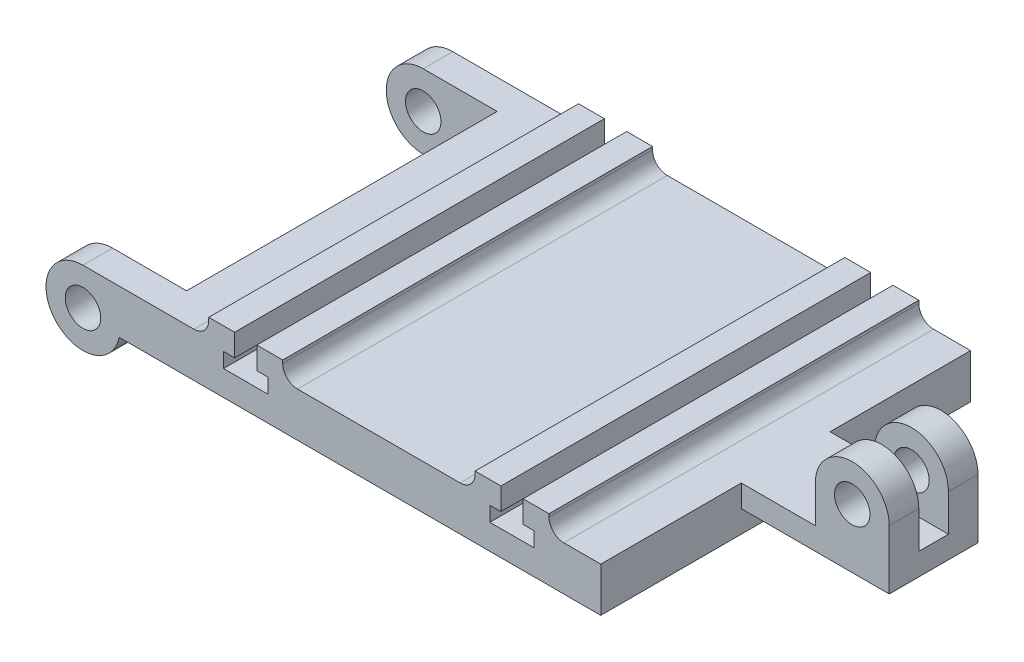
SolidWorks part; units mm, degrees
material "Ferro fundido maleável"
ref_plane "Plano frontal" through (0, 0, 0) normal (0, 0, 1) x (1, 0, 0)
ref_plane "Plano superior" through (0, 0, 0) normal (0, 1, 0) x (1, 0, 0)
ref_plane "Plano direito" through (0, 0, 0) normal (1, 0, 0) x (0, 0, -1)
sketch "Esboço1" plane through (0, 0, 0) normal (0, 1, 0) x (1, 0, 0)
  line L1 (-150, -125) -> (150, -125)
  line L2 (-150, -125) -> (-150, 125)
  line L3 (-150, 125) -> (150, 125)
  line L4 (150, -125) -> (150, 125)
  line L5 (-150, -125) -> (150, 125) construction
  line L6 (-150, 125) -> (150, -125) construction
  point P0 (0, 0)
  dimension "D1" = 300
  dimension "D2" = 250
extrude "Ressalto-extrusão1" add sketch "Esboço1" along normal blind 30
sketch "Esboço3" plane through (0, 30, 0) normal (0, 1, 0) x (1, 0, 0)
  line L0 (150, 125) -> (-150, 125) construction
  line L1 (115, 125) -> (65, 125)
  line L2 (115, 125) -> (115, -125)
  line L3 (115, -125) -> (65, -125)
  line L4 (65, 125) -> (65, -125)
  line L5 (-150, -125) -> (150, -125) construction
  line L6 (0, 0) -> (0, 25.318) construction
  line L7 (-65, 125) -> (-65, -125)
  line L8 (-115, -125) -> (-65, -125)
  line L9 (-115, 125) -> (-115, -125)
  line L10 (-115, 125) -> (-65, 125)
  dimension "D1" = 130
  dimension "D2" = 50
extrude "Ressalto-extrusão2" add sketch "Esboço3" along normal blind 12
fillet "Filete1" radius 10 4 edges at (-115, 30, 0) (-65, 30, 0)
sketch "Esboço4" plane through (0, 0, 0) normal (0, 0, 1) x (1, 0, 0)
  line L0 (90, 42) -> (90, 17) construction
  line L1 (65, 42) -> (115, 42) construction
  line L2 (0, 0) -> (0, 30) construction
  line L3 (-55, 30) -> (55, 30) construction
  line L4 (82.5, 42) -> (97.5, 42)
  line L5 (97.5, 42) -> (97.5, 27)
  line L6 (97.5, 27) -> (105, 27)
  line L7 (105, 27) -> (105, 17)
  line L8 (105, 17) -> (75, 17)
  line L9 (75, 27) -> (75, 17)
  line L10 (82.5, 27) -> (75, 27)
  line L11 (82.5, 42) -> (82.5, 27)
  line L12 (-90, 42) -> (-90, 17) construction
  line L13 (-82.5, 42) -> (-82.5, 27)
  line L14 (-82.5, 27) -> (-75, 27)
  line L15 (-75, 27) -> (-75, 17)
  line L16 (-105, 17) -> (-75, 17)
  line L17 (-105, 27) -> (-105, 17)
  line L18 (-97.5, 27) -> (-105, 27)
  line L19 (-97.5, 42) -> (-97.5, 27)
  line L20 (-82.5, 42) -> (-97.5, 42)
  dimension "D1" = 25
  dimension "D2" = 15
  dimension "D3" = 30
  dimension "D4" = 10
extrude "Corte-extrusão1" cut sketch "Esboço4" against normal up to next and the other way up to next
sketch "Esboço5" plane through (0, 0, 0) normal (0, 0, 1) x (1, 0, 0)
  line L0 (150, 30) -> (200, 30)
  line L1 (200, 30) -> (200, 55)
  line L2 (150, 30) -> (150, 15)
  line L3 (150, 15) -> (250, 15)
  line L4 (250, 55) -> (250, 15)
  arc A0 (200, 55) -> (250, 55) centre (225, 55) cw
  circle A1 centre (225, 55) radius 12
  dimension "D3" = 25
  dimension "D5" = 24
  dimension "D1" = 15
  dimension "D2" = 100
  dimension "D4" = 25
extrude "Ressalto-extrusão3" add sketch "Esboço5" along normal mid plane 60
sketch "Esboço6" plane through (0, 0, 0) normal (0, 0, 1) x (1, 0, 0)
  line L1 (200, 30) -> (260.2149, 30)
  line L2 (200, 30) -> (200, 96.5975)
  line L3 (200, 96.5975) -> (260.2149, 96.5975)
  line L4 (260.2149, 30) -> (260.2149, 96.5975)
extrude "Corte-extrusão2" cut sketch "Esboço6" against normal mid plane 20
sketch "Esboço7" plane through (0, 0, 125) normal (0, 0, 1) x (1, 0, 0)
  line L0 (-150, 30) -> (-200, 30)
  line L1 (-175.5051, 0) -> (-150, 0)
  line L2 (-150, 0) -> (-150, 30)
  arc A0 (-200, 30) -> (-175.5051, 0) centre (-200, 5) ccw
  circle A1 centre (-200, 5) radius 12
  dimension "D1" = 25
  dimension "D2" = 24
  dimension "D3" = 50
extrude "Ressalto-extrusão4" add sketch "Esboço7" against normal blind 20
mirror "Espelhar1" about plane through (0, 0, 0) normal (0, 0, 1) of "Ressalto-extrusão4"
sketch "Esboço8" plane through (0, 0, 0) normal (0, -1, 0) x (1, 0, 0)
  line L0 (-175.5051, 125) -> (150, 125) construction
  line L1 (-130, -105) -> (130, -105)
  line L2 (-130, -105) -> (-130, 105)
  line L3 (-130, 105) -> (130, 105)
  line L4 (130, -105) -> (130, 105)
  line L5 (-130, -105) -> (130, 105) construction
  line L6 (-130, 105) -> (130, -105) construction
  line L7 (-150, -105) -> (-150, 105) construction
  point P0 (0, 0)
  dimension "D1" = 20
  dimension "D2" = 20
extrude "Corte-extrusão3" cut sketch "Esboço8" against normal blind 10
